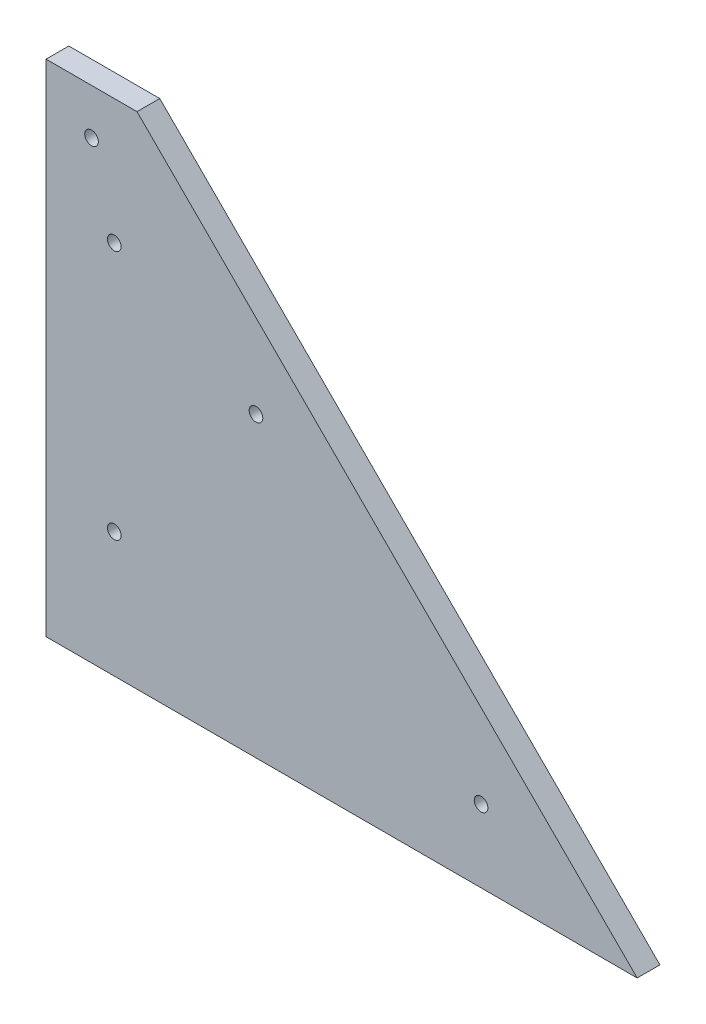
SolidWorks part; units mm, degrees
material "Polywood"
ref_plane "Front Plane" through (0, 0, 0) normal (0, 0, 1) x (1, 0, 0)
ref_plane "Top Plane" through (0, 0, 0) normal (0, 1, 0) x (1, 0, 0)
ref_plane "Right Plane" through (0, 0, 0) normal (1, 0, 0) x (0, 0, -1)
sketch "Sketch1" plane through (0, 0, 0) normal (0, 0, 1) x (1, 0, 0)
  line L0 (0, 0) -> (0, 110)
  line L1 (0, 0) -> (130, 0)
  line L2 (0, 110) -> (20, 110)
  line L3 (20, 110) -> (130, 0)
  dimension "D1" = 110
  dimension "D2" = 135
  dimension "D3" = 20
extrude "Boss-Extrude1" add sketch "Sketch1" along normal blind 5
sketch "Sketch2" plane through (0, 0, 5) normal (0, 0, 1) x (1, 0, 0)
  line L0 (0, 55) -> (50000, 55) construction
  line L1 (0, 110) -> (0, 0) construction
  circle A0 centre (15, 82.5) radius 1.5
  circle A1 centre (15, 27.5) radius 1.5
  point P6 (0, 55)
  dimension "D2" = 3
  dimension "D1" = 15
  dimension "D3" = 27.5
extrude "Cut-Extrude1" cut sketch "Sketch2" against normal through all
sketch "Sketch3" plane through (0, 0, 5) normal (0, 0, 1) x (1, 0, 0)
  line L0 (130, 0) -> (20, 110) construction
  line L1 (20, 110) -> (-33872.8051, -33782.8051) construction
  line L2 (55.2512, 74.5405) -> (-33837.554, -33818.2646) construction
  line L3 (102.2712, 72.0631) -> (-35253.0678, -35283.276) construction
  circle A0 centre (46.163, 65.4523) radius 1.5
  circle A1 centre (95.6604, 15.9548) radius 1.5
  dimension "D1" = 3
  dimension "D2" = 13
  dimension "D3" = 50
  dimension "D4" = 35
extrude "Cut-Extrude2" cut sketch "Sketch3" against normal through all
sketch "Sketch4" plane through (0, 0, 5) normal (0, 0, 1) x (1, 0, 0)
  line L0 (20, 110) -> (0, 110) construction
  line L1 (0, 110) -> (0, 0) construction
  circle A0 centre (10, 100) radius 1.5
  dimension "D1" = 3
  dimension "D2" = 10
  dimension "D3" = 10
extrude "Cut-Extrude3" cut sketch "Sketch4" against normal through all
